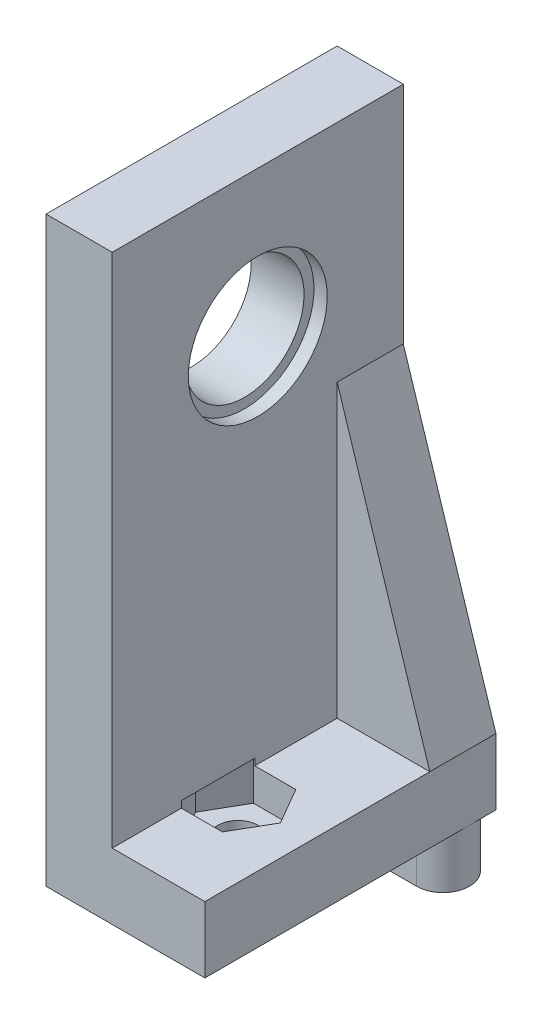
SolidWorks part; units mm, degrees
material "1060 合金"
ref_plane "前视基准面" through (0, 0, 0) normal (0, 0, 1) x (1, 0, 0)
ref_plane "上视基准面" through (0, 0, 0) normal (0, 1, 0) x (1, 0, 0)
ref_plane "右视基准面" through (0, 0, 0) normal (1, 0, 0) x (0, 0, -1)
sketch "草图1" plane through (0, 0, 0) normal (1, 0, 0) x (0, 0, -1)
  line L1 (-11, 17) -> (29, 17)
  line L2 (-11, 17) -> (-11, -27)
  line L3 (-11, -27) -> (29, -27)
  line L4 (29, 17) -> (29, -27)
  circle A6 centre (0, 0) radius 4.5
  circle A7 centre (18, 6) radius 4.5
  circle A8 centre (11.5439, -13.3514) radius 4.5
  dimension "D1" = 20.4
  dimension "D2" = 18.9737
  dimension "D3" = 17.65
  dimension "D4" = 9
  dimension "D5" = 9
  dimension "D7" = 11
  dimension "D6" = 11
  dimension "D8" = 18
  dimension "D9" = 27
  dimension "D10" = 11
extrude "凸台-拉伸1" add sketch "草图1" along normal blind 5
sketch "草图2" plane through (5, 0, 0) normal (-1, 0, 0) x (0, 0, 1)
  circle A0 centre (-18, 6) radius 5.25
  circle A1 centre (0, 0) radius 5.25
extrude "切除-拉伸1" cut sketch "草图2" along normal blind 1
sketch "草图3" plane through (5, 0, 0) normal (1, 0, 0) x (0, 0, -1)
  line L0 (-11, -27) -> (29, -27) construction
  line L1 (-11, 17) -> (7, 17)
  line L2 (-11, 17) -> (-11, -27)
  line L3 (-11, -27) -> (7, -27)
  line L4 (7, 17) -> (7, -27)
  circle A0 centre (18, 6) radius 4.5 construction
  dimension "D1" = 11
extrude "切除-拉伸2" cut sketch "草图3" against normal through all
sketch "草图4" plane through (5, 0, 0) normal (1, 0, 0) x (0, 0, -1)
  circle A0 centre (11.5439, -13.3514) radius 4.5
extrude "凸台-拉伸2" add sketch "草图4" against normal through all
sketch "草图5" plane through (5, 0, 0) normal (1, 0, 0) x (0, 0, -1)
  line L0 (29, -27) -> (29, 17) construction
  line L1 (7, -27) -> (29, -27)
  line L2 (7, -27) -> (7, -22)
  line L3 (7, -22) -> (29, -22)
  line L4 (29, -27) -> (29, -22)
  dimension "D1" = 5
extrude "凸台-拉伸3" add sketch "草图5" along normal blind 7
sketch "草图6" plane through (0, -27, 0) normal (0, -1, 0) x (1, 0, 0)
  line L1 (0, -29) -> (10, -29)
  line L2 (0, -29) -> (0, -25)
  line L3 (0, -25) -> (10, -25)
  arc A0 (10, -29) -> (10, -25) centre (10, -27) ccw
  dimension "D1" = 4
  dimension "D2" = 10
  dimension "D3" = 10
extrude "凸台-拉伸4" add sketch "草图6" along normal blind 4
sketch "草图7" plane through (0, -27, 0) normal (0, -1, 0) x (1, 0, 0)
  line L0 (0, -7) -> (0, -25) construction
  line L1 (0, -7) -> (12, -7) construction
  circle A0 centre (6.5, -15) radius 1.5
  dimension "D3" = 3
  dimension "D1" = 6.5
  dimension "D2" = 8
extrude "切除-拉伸3" cut sketch "草图7" against normal blind 5
sketch "草图8" plane through (0, -22, 0) normal (0, 1, 0) x (-1, 0, 0)
  line L1 (-9.7043, -15) -> (-8.1021, -17.775)
  line L2 (-8.1021, -17.775) -> (-4.8979, -17.775)
  line L3 (-4.8979, -17.775) -> (-3.2957, -15)
  line L4 (-3.2957, -15) -> (-4.8979, -12.225)
  line L5 (-4.8979, -12.225) -> (-8.1021, -12.225)
  line L6 (-8.1021, -12.225) -> (-9.7043, -15)
  circle A0 centre (-6.5, -15) radius 2.775 construction
  dimension "D1" = 5.55
extrude "切除-拉伸4" cut sketch "草图8" against normal blind 2.5 and the other way blind 0.5
sketch "草图9" plane through (0, 0, -29) normal (0, 0, -1) x (-1, 0, 0)
  line L0 (-5, -22) -> (-12, -22)
  line L1 (-12, -22) -> (-5, 0)
  line L2 (-5, -22) -> (-5, 17) construction
  line L3 (-5, 0) -> (-5, -22)
  dimension "D1" = 22
extrude "凸台-拉伸5" add sketch "草图9" against normal blind 5
